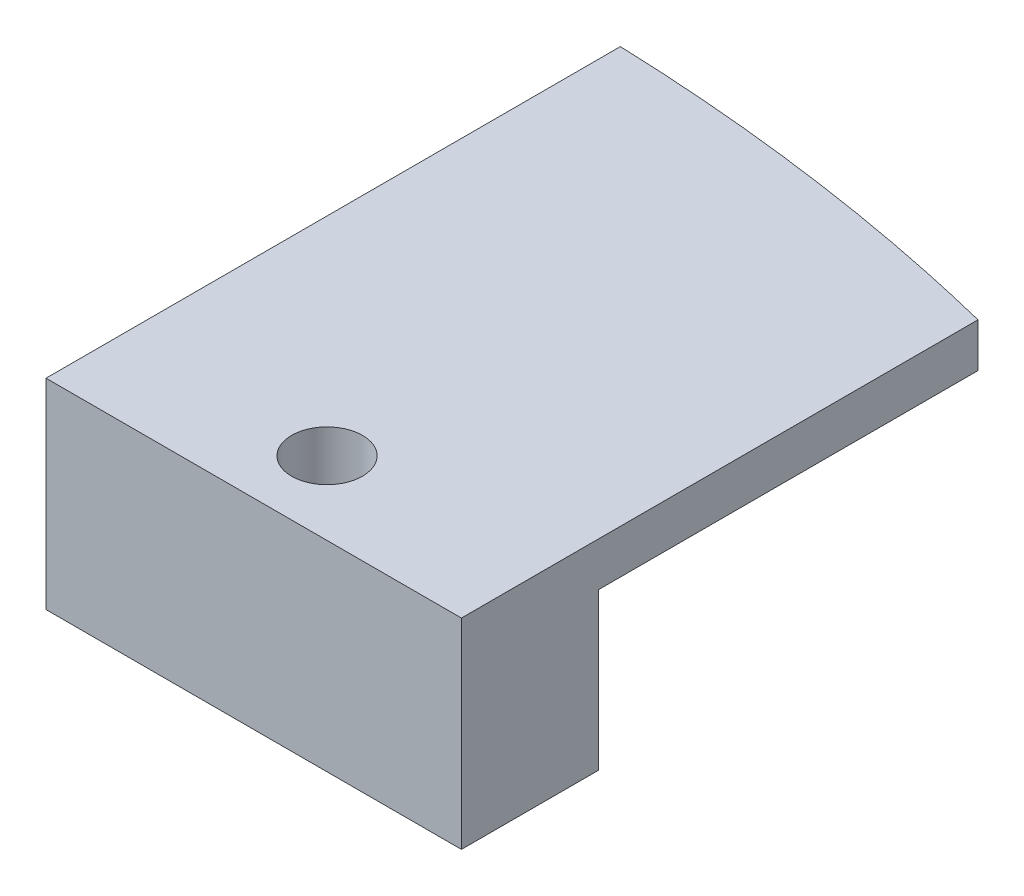
SolidWorks part; units mm, degrees
ref_plane "Front Plane" through (0, 0, 0) normal (0, 0, 1) x (1, 0, 0)
ref_plane "Top Plane" through (0, 0, 0) normal (0, 1, 0) x (1, 0, 0)
ref_plane "Right Plane" through (0, 0, 0) normal (1, 0, 0) x (0, 0, -1)
sketch "Sketch1" plane through (0, 0, 0) normal (0, 1, 0) x (1, 0, 0)
  line L0 (0, 15) -> (0, 0)
  line L1 (0, 0) -> (17, 0)
  line L2 (17, 0) -> (17, 10)
  line L3 (17, 10) -> (0, 15)
  dimension "D1" = 17
  dimension "D2" = 15
  dimension "D3" = 10
extrude "Boss-Extrude1" add sketch "Sketch1" along normal blind 1.8
sketch "Sketch3" plane through (0, 1.8, 0) normal (0, 1, 0) x (1, 0, 0)
  line L0 (0, 15) -> (0, 0) construction
  line L1 (0, 15) -> (0, 5.5044)
  line L2 (17, 10) -> (0, 15) construction
  line L3 (17, 10) -> (0, 15)
  line L4 (17, 0) -> (17, 10) construction
  line L5 (17, 3.1386) -> (17, 10)
  ellipse E0 centre (-6.646, -59.7673) end of major axis (-80.5066, -72.7909) minor radius 65 construction
  ellipse E1 centre (-6.646, -59.7673) end of major axis (-80.5066, -72.7909) minor radius 65 (17, 3.1386) -> (0, 5.5044) ccw
extrude "Cut-Extrude2" cut sketch "Sketch3" against normal up to next
ref_plane "Plane1" through (0, 1.8, 0) normal (1, 0, 0) x (0, 0, -1)
sketch "Sketch5" plane through (0, 1.8, 0) normal (0, 1, 0) x (1, 0, 0)
  line L0 (17, 0) -> (17, -18)
  line L1 (17, -18) -> (0, -18)
  line L2 (0, -18) -> (0, 0)
  line L3 (0, 0) -> (17, 0) construction
  line L4 (0, 0) -> (17, 0)
  line L5 (0, -2.6) -> (0, 5.5044) construction
  dimension "D1" = 18
extrude "Boss-Extrude2" add sketch "Sketch5" against normal up to vertex (1.8 mm away)
sketch "Sketch6" plane through (0, 0, 0) normal (0, -1, 0) x (1, 0, 0)
  line L0 (0, 18) -> (17, 18) construction
  line L1 (0, 18) -> (17, 18)
  line L2 (0, -5.5044) -> (0, 18) construction
  line L3 (0, 12.4) -> (0, 18)
  line L4 (17, 18) -> (17, -3.1386) construction
  line L5 (17, 18) -> (17, 12.4)
  line L7 (0, 12.4) -> (17, 12.4)
  dimension "D1" = 5.6
extrude "Boss-Extrude3" add sketch "Sketch6" along normal blind 6.4
sketch "Sketch7" plane through (0, 1.8, 0) normal (0, 1, 0) x (1, 0, 0)
  line L0 (8.5, -18) -> (8.5, -15) construction
  line L1 (0, -18) -> (17, -18) construction
  line L3 (0, 5.5044) -> (0, -18) construction
  circle A0 centre (8.5, -15) radius 1.45
  point P6 (9.064, -15.1257)
  dimension "D1" = 2.9
  dimension "D2" = 3
extrude "Cut-Extrude3" cut sketch "Sketch7" against normal up to next
